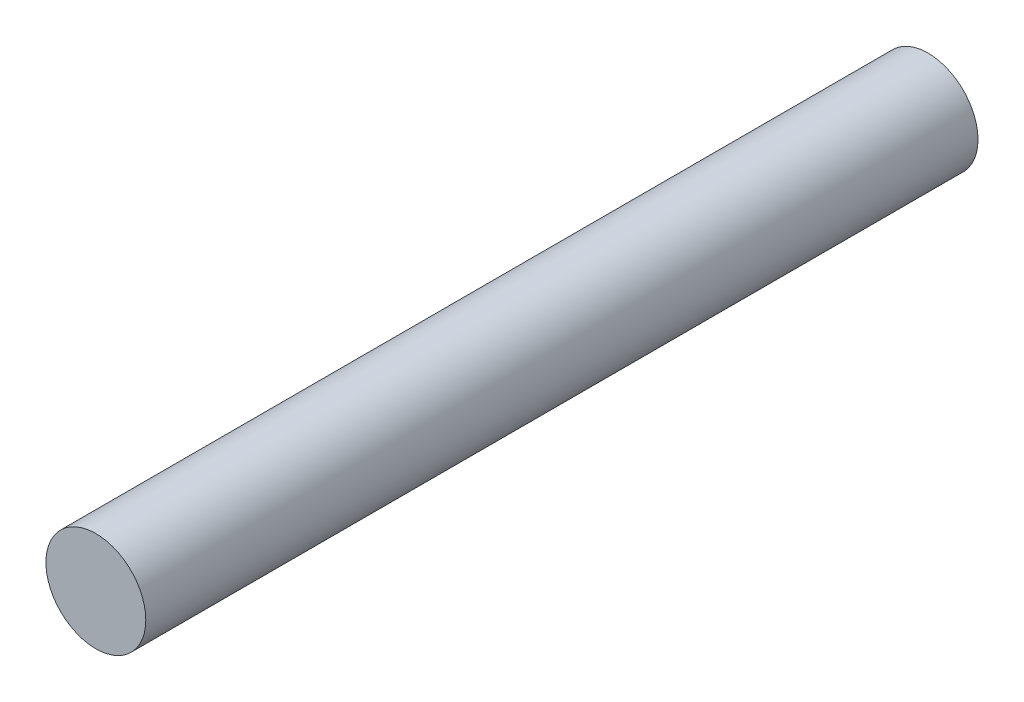
SolidWorks part; units mm, degrees
ref_plane "Front Plane" through (0, 0, 0) normal (0, 0, 1) x (1, 0, 0)
ref_plane "Top Plane" through (0, 0, 0) normal (0, 1, 0) x (1, 0, 0)
ref_plane "Right Plane" through (0, 0, 0) normal (1, 0, 0) x (0, 0, -1)
sketch "Esquisse1" plane through (0, 0, 0) normal (0, 0, 1) x (1, 0, 0)
  circle A0 centre (0, 0) radius 3
  dimension "D1" = 6
extrude "Boss.-Extru.1" add sketch "Esquisse1" along normal blind 50
